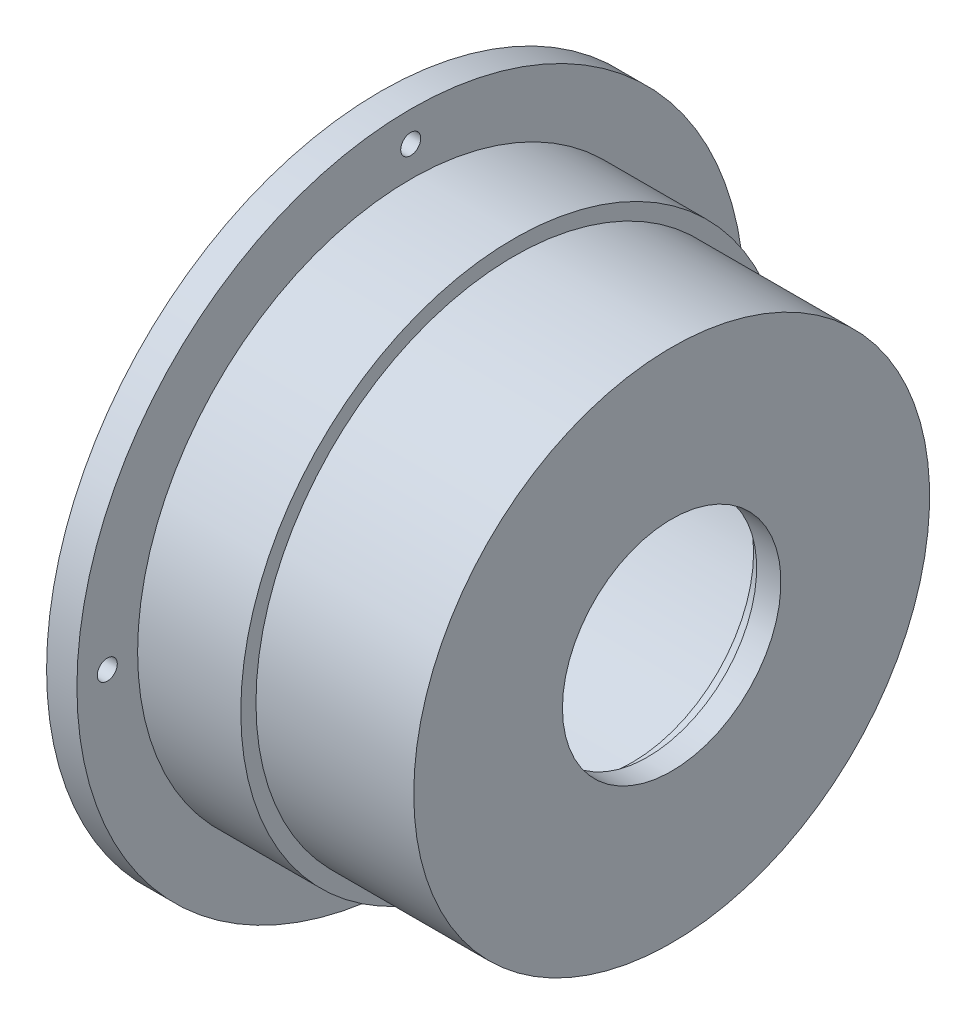
SolidWorks part; units mm, degrees
material "1060 Alloy"
ref_plane "Front Plane" through (0, 0, 0) normal (0, 0, 1) x (1, 0, 0)
ref_plane "Top Plane" through (0, 0, 0) normal (0, 1, 0) x (1, 0, 0)
ref_plane "Right Plane" through (0, 0, 0) normal (1, 0, 0) x (0, 0, -1)
sketch "Sketch2" plane through (0, 0, 0) normal (0, 0, 1) x (1, 0, 0)
  line L0 (-64.1034, 0) -> (113.4236, 0) construction
  line L2 (0, 37.6) -> (41.5, 37.6)
  line L3 (0, -55) -> (0, 55) construction
  line L13 (41.5, 37.6) -> (41.5, 20)
  line L14 (41.5, 20) -> (44, 20)
  line L19 (22, 42.5) -> (22, 45)
  line L21 (0, 45) -> (0, 37.6)
  line L25 (48, 42.5) -> (22, 42.5)
  line L26 (22, 45) -> (5, 45)
  line L27 (5, 45) -> (5, 55)
  line L28 (5, 55) -> (0, 55)
  line L29 (0, 55) -> (0, 45)
  line L30 (44, 20) -> (44, 18)
  line L31 (44, 18) -> (48, 18)
  line L32 (48, 18) -> (48, 42.5)
  point P14 (42.75, 20)
  dimension "D1" = 37.6
  dimension "D2" = 41.5
  dimension "D3" = 20
  dimension "D4" = 2.5
  dimension "D5" = 42.5
  dimension "D6" = 45
  dimension "D7" = 5
  dimension "D8" = 55
  dimension "D9" = 22
  dimension "D10" = 18
  dimension "D11" = 4
revolve "Revolve1" add sketch "Sketch2" angle 360 about L0
ref_plane "Plane1" through (47, 0, 0) normal (1, 0, 0) x (0, 0, -1)
hole_wizard "M4x0.7 Tapped Hole1" positions "Sketch10" profile "Sketch11" tap size "M4x0.7" standard "ANSI Metric" end condition through all
sketch "Sketch10" plane through (0, 0, 0) normal (-1, 0, 0) x (0, 0, 1)
  circle A0 centre (0, 0) radius 50
  point P0 (0, 50)
  point P2 (50, 0)
  point P4 (0, -50)
  point P6 (-50, 0)
  dimension "D1" = 100
sketch "Sketch11" plane through (0, 50, 0) normal (0, 1, 0) x (0, 0, 1)
  line L0 (0, 0) -> (0, 48)
  line L1 (0, 48) -> (1.65, 48)
  line L2 (1.65, 48) -> (1.65, 0)
  line L5 (1.65, 0) -> (0, 0)
  line L11 (0, -6.35) -> (0, 107.95) construction
  dimension "Thread Major Dia." = 3.3
  dimension "Thru Tap Drill Depth" = 48
